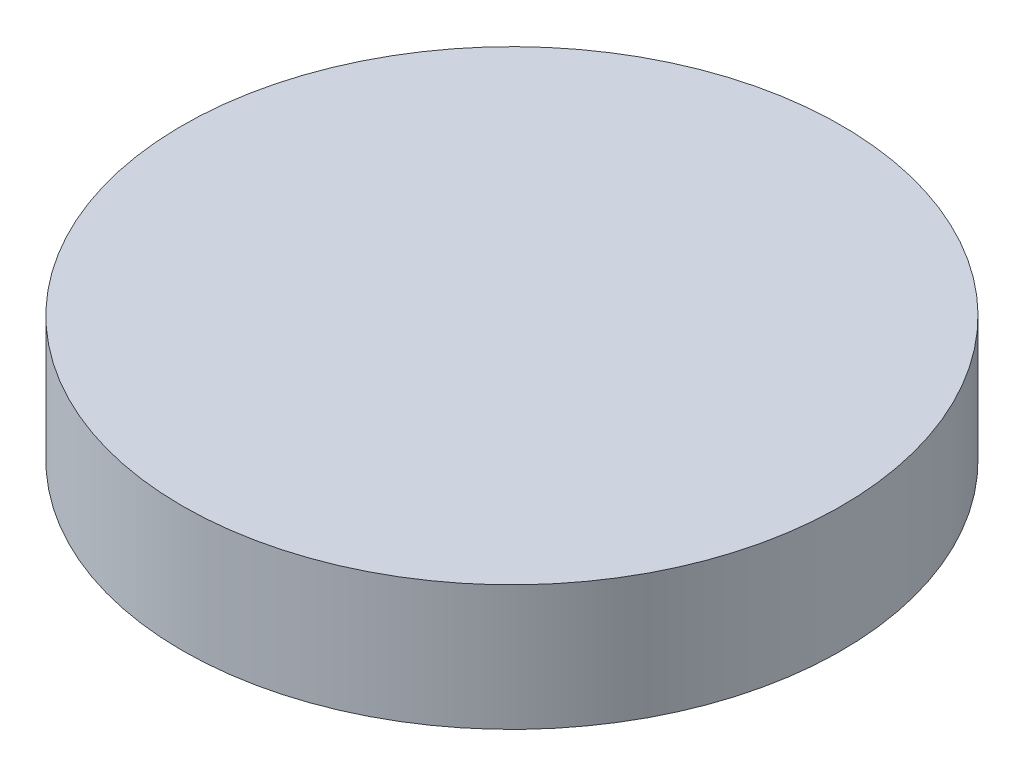
SolidWorks part; units mm, degrees
ref_plane "Front Plane" through (0, 0, 0) normal (0, 0, 1) x (1, 0, 0)
ref_plane "Top Plane" through (0, 0, 0) normal (0, 1, 0) x (1, 0, 0)
ref_plane "Right Plane" through (0, 0, 0) normal (1, 0, 0) x (0, 0, -1)
sketch "Sketch1" plane through (0, 0, 0) normal (0, 1, 0) x (1, 0, 0)
  circle A0 centre (0, 0) radius 150
  dimension "D1" = 300
extrude "Extrude1" add sketch "Sketch1" along normal blind 57
